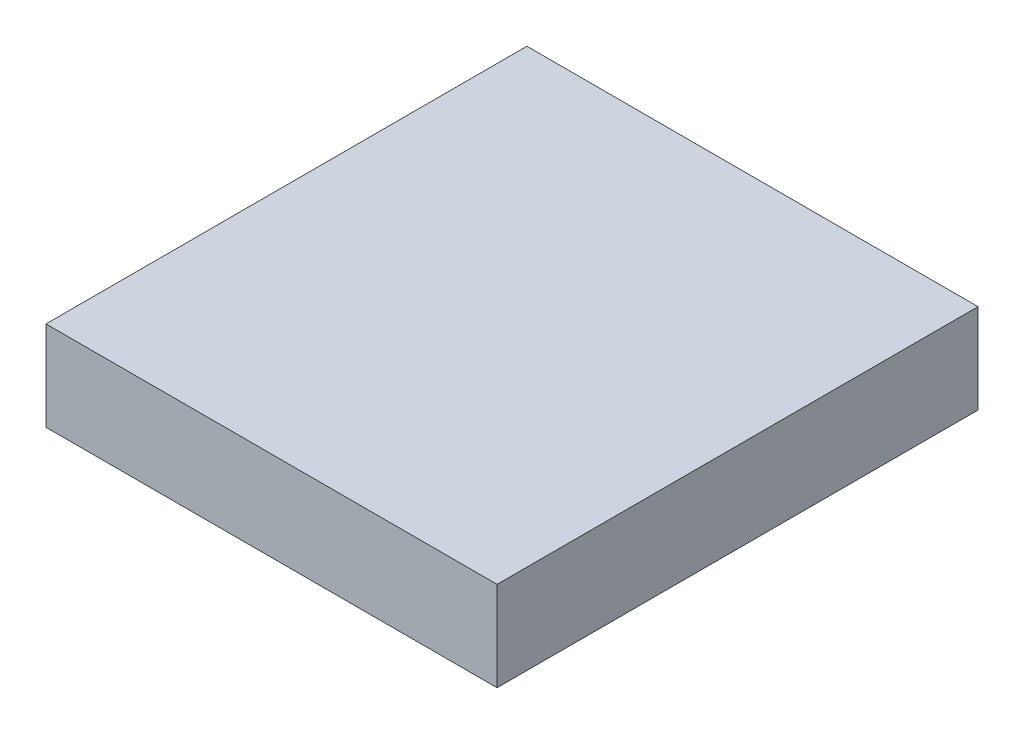
SolidWorks part; units mm, degrees
ref_plane "Front Plane" through (0, 0, 0) normal (0, 0, 1) x (1, 0, 0)
ref_plane "Top Plane" through (0, 0, 0) normal (0, 1, 0) x (1, 0, 0)
ref_plane "Right Plane" through (0, 0, 0) normal (1, 0, 0) x (0, 0, -1)
sketch "Sketch1" plane through (0, 0, 0) normal (0, 1, 0) x (1, 0, 0)
  line L1 (-215.9, -230.1875) -> (215.9, -230.1875)
  line L2 (-215.9, -230.1875) -> (-215.9, 230.1875)
  line L3 (-215.9, 230.1875) -> (215.9, 230.1875)
  line L4 (215.9, -230.1875) -> (215.9, 230.1875)
  line L5 (-215.9, -230.1875) -> (215.9, 230.1875) construction
  line L6 (-215.9, 230.1875) -> (215.9, -230.1875) construction
  point P0 (0, 0)
  dimension "D1" = 460.375
  dimension "D2" = 431.8
extrude "Boss-Extrude1" add sketch "Sketch1" along normal blind 85.725
